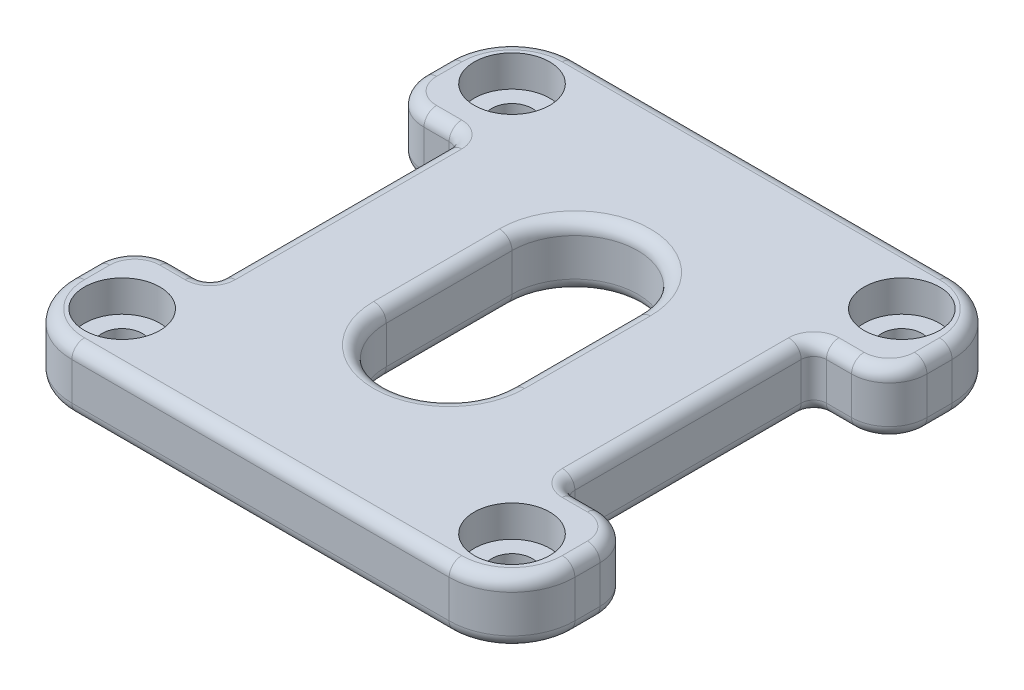
SolidWorks part; units mm, degrees
ref_plane "前视基准面" through (0, 0, 0) normal (0, 0, 1) x (1, 0, 0)
ref_plane "上视基准面" through (0, 0, 0) normal (0, 1, 0) x (1, 0, 0)
ref_plane "右视基准面" through (0, 0, 0) normal (1, 0, 0) x (0, 0, -1)
sketch "草图1" plane through (0, 0, 0) normal (0, 1, 0) x (1, 0, 0)
  line L1 (-20, -20) -> (20, -20)
  line L2 (-20, -20) -> (-20, 20)
  line L3 (-20, 20) -> (20, 20)
  line L4 (20, -20) -> (20, 20)
  line L5 (-20, -20) -> (20, 20) construction
  line L6 (-20, 20) -> (20, -20) construction
  point P0 (0, 0)
  dimension "D1" = 40
  dimension "D2" = 40
extrude "凸台-拉伸1" add sketch "草图1" along normal blind 5
sketch "草图2" plane through (0, 5, 0) normal (0, 1, 0) x (1, 0, 0)
  circle A0 centre (-15.5, 15.5) radius 1.6
  circle A1 centre (15.5, 15.5) radius 1.6
  circle A2 centre (15.5, -15.5) radius 1.6
  circle A3 centre (-15.5, -15.5) radius 1.6
  dimension "D1" = 3.2
  dimension "D2" = 3.2
  dimension "D3" = 3.2
  dimension "D4" = 3.2
  dimension "D5" = 15.5
  dimension "D6" = 15.5
  dimension "D7" = 15.5
  dimension "D8" = 15.5
  dimension "D9" = 15.5
  dimension "D10" = 15.5
  dimension "D11" = 15.5
  dimension "D12" = 15.5
extrude "切除-拉伸1" cut sketch "草图2" against normal through all
fillet "圆角1" radius 5 4 edges at (20, 2.5, 20) (-20, 2.5, 20) (20, 2.5, -20) (-20, 2.5, -20)
sketch "草图3" plane through (0, 5, 0) normal (0, 1, 0) x (1, 0, 0)
  line L1 (-24, -10) -> (-14, -10)
  line L2 (-24, -10) -> (-24, 10)
  line L3 (-24, 10) -> (-14, 10)
  line L4 (-14, -10) -> (-14, 10)
  line L5 (-24, -10) -> (-14, 10) construction
  line L6 (-24, 10) -> (-14, -10) construction
  line L7 (24, -10) -> (14, -10)
  line L8 (24, -10) -> (24, 10)
  line L9 (24, 10) -> (14, 10)
  line L10 (14, -10) -> (14, 10)
  line L11 (24, -10) -> (14, 10) construction
  line L12 (24, 10) -> (14, -10) construction
  point P0 (-19, 0)
  point P5 (19, 0)
  dimension "D1" = 0
  dimension "D2" = 0
  dimension "D3" = 10
  dimension "D4" = 10
  dimension "D5" = 20
  dimension "D6" = 20
  dimension "D7" = 14
  dimension "D8" = 14
extrude "切除-拉伸2" cut sketch "草图3" against normal through all
fillet "圆角2" radius 1 4 edges at (14, 2.5, -10) (14, 2.5, 10) (-14, 2.5, 10) (-14, 2.5, -10)
fillet "圆角3" radius 3 4 edges at (20, 2.5, 10) (20, 2.5, -10) (-20, 2.5, 10) (-20, 2.5, -10)
sketch "草图4" plane through (0, 5, 0) normal (0, 1, 0) x (1, 0, 0)
  circle A0 centre (-15.5, 15.5) radius 3
  circle A1 centre (15.5, 15.5) radius 3
  circle A2 centre (15.5, -15.5) radius 3
  circle A3 centre (-15.5, -15.5) radius 3
  dimension "D1" = 6
  dimension "D2" = 6
  dimension "D3" = 6
  dimension "D4" = 6
extrude "切除-拉伸3" cut sketch "草图4" against normal blind 2.5
fillet "圆角5" radius 1 48 edges at (14.2929, 5, -9.7071) (16, 5, -10) (19.1213, 5, -10.8787) (20, 5, -14) (18.5355, 5, -18.5355) (0, 5, -20) (-18.5355, 5, -18.5355) (-20, 5, -14) (-19.1213, 5, -10.8787) (-16, 5, -10) (-14.2929, 5, -9.7071) (-14, 5, 0) (-14.2929, 5, 9.7071) (-16, 5, 10) (-19.1213, 5, 10.8787) (-20, 5, 14) (-18.5355, 5, 18.5355) (0, 5, 20) (18.5355, 5, 18.5355) (20, 5, 14) (19.1213, 5, 10.8787) (16, 5, 10) (14.2929, 5, 9.7071) (14.2929, 0, -9.7071) (16, 0, -10) (19.1213, 0, -10.8787) (20, 0, -14) (18.5355, 0, -18.5355) (0, 0, -20) (-18.5355, 0, -18.5355) (-20, 0, -14) (-19.1213, 0, -10.8787) (-16, 0, -10) (-14.2929, 0, -9.7071) (-14, 0, 0) (-14.2929, 0, 9.7071) (-16, 0, 10) (-19.1213, 0, 10.8787) (-20, 0, 14) (-18.5355, 0, 18.5355) (0, 0, 20) (18.5355, 0, 18.5355) (20, 0, 14) (19.1213, 0, 10.8787) (16, 0, 10) (14.2929, 0, 9.7071) (14, 5, 0) (14, 0, 0)
sketch "草图5" plane through (0, 5, 0) normal (0, 1, 0) x (1, 0, 0)
  line L0 (0, -5) -> (0, 5) construction
  line L1 (-5, -5) -> (-5, 5)
  line L2 (5, -5) -> (5, 5)
  arc A1 (-5, -5) -> (5, -5) centre (0, -5) ccw
  arc A2 (5, 5) -> (-5, 5) centre (0, 5) ccw
  point P3 (0, 0)
  dimension "D1" = 10
  dimension "D2" = 5
extrude "切除-拉伸4" cut sketch "草图5" against normal through all
fillet "圆角6" radius 1 8 edges at (5, 0, 0) (0, 0, 10) (-5, 0, 0) (5, 5, 0) (0, 5, 10) (-5, 5, 0) (0, 0, -10) (0, 5, -10)
